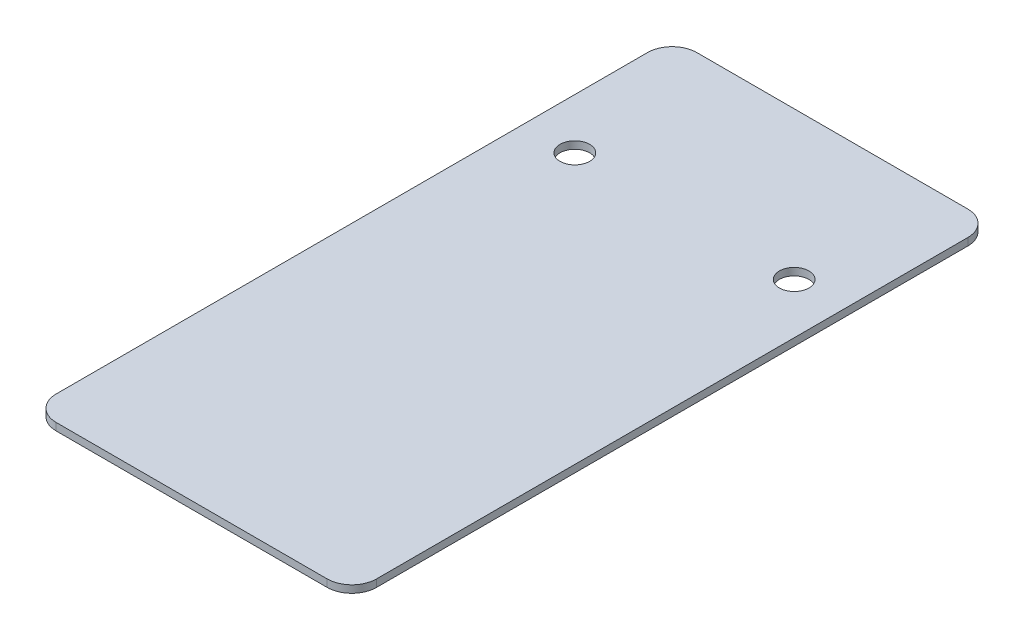
SolidWorks part; units mm, degrees
ref_plane "Front Plane" through (0, 0, 0) normal (0, 0, 1) x (1, 0, 0)
ref_plane "Top Plane" through (0, 0, 0) normal (0, 1, 0) x (1, 0, 0)
ref_plane "Right Plane" through (0, 0, 0) normal (1, 0, 0) x (0, 0, -1)
sketch "Sketch1" plane through (0, 0, 0) normal (0, 1, 0) x (1, 0, 0)
  line L1 (-65, -60) -> (65, -60)
  line L2 (-65, -60) -> (-65, 60)
  line L3 (-65, 60) -> (65, 60)
  line L4 (65, -60) -> (65, 60)
  line L5 (-65, -60) -> (65, 60) construction
  line L6 (-65, 60) -> (65, -60) construction
  point P0 (0, 0)
  dimension "D1" = 130
  dimension "D2" = 120
extrude "Boss-Extrude1" add sketch "Sketch1" along normal blind 3
sketch "Sketch2" plane through (0, 3, 0) normal (0, 1, 0) x (1, 0, 0)
  circle A0 centre (44.5, 0) radius 6
  dimension "D1" = 12
  dimension "D2" = 44.5
extrude "Cut-Extrude1" cut sketch "Sketch2" against normal through all both and the other way through all
mirror "Mirror1" about plane through (0, 0, 0) normal (1, 0, 0) of "Cut-Extrude1"
sketch "Sketch3" plane through (0, 0, 60) normal (0, 0, 1) x (1, 0, 0)
  line L4 (-65, 0) -> (65, 0)
  line L5 (65, 0) -> (65, 3)
  line L6 (65, 3) -> (-65, 3)
  line L7 (-65, 3) -> (-65, 0)
  line L8 (-65, 0) -> (65, 0)
  line L9 (65, 0) -> (65, 3)
  line L10 (65, 3) -> (-65, 3)
  line L11 (-65, 3) -> (-65, 0)
  dimension "D1" = 0
extrude "Boss-Extrude2" add sketch "Sketch3" along normal blind 140
fillet "Fillet1" radius 10 4 edges at (-65, 1.5, 200) (65, 1.5, 200) (65, 1.5, -60) (-65, 1.5, -60)
